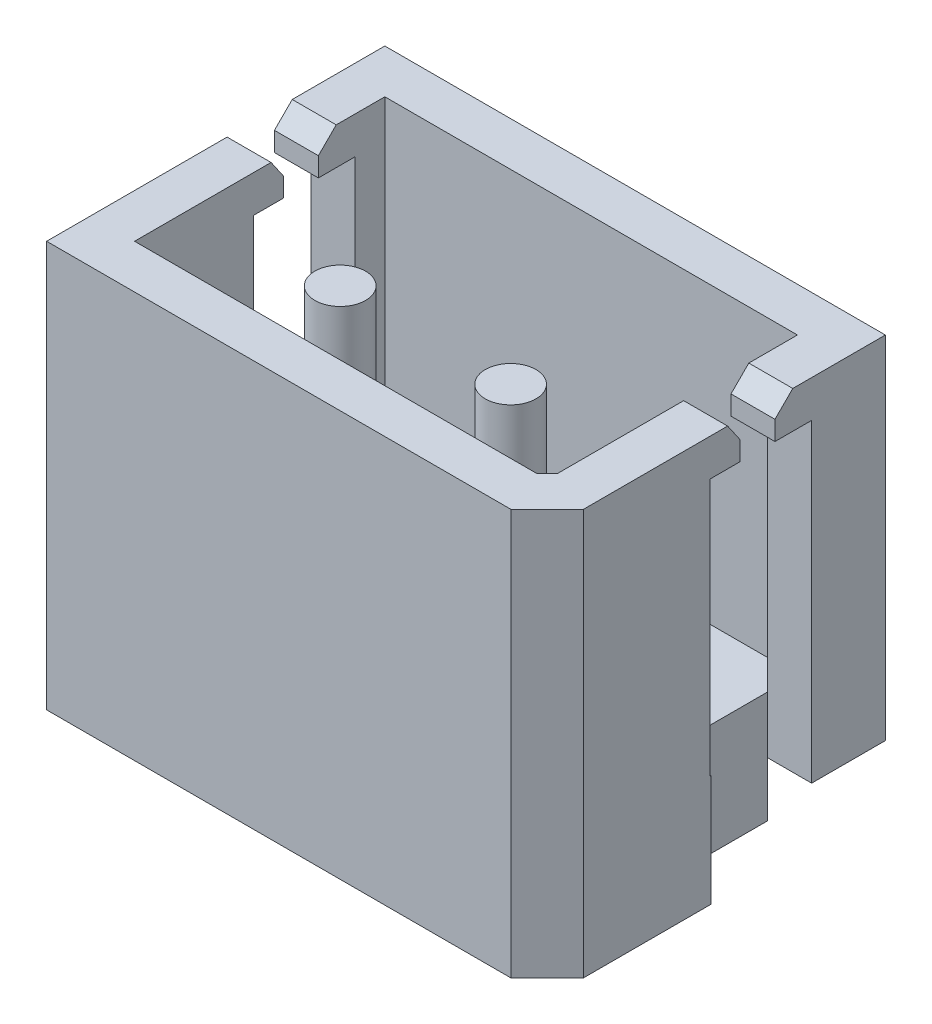
SolidWorks part; units mm, degrees
ref_plane "Front Plane" through (0, 0, 0) normal (0, 0, 1) x (1, 0, 0)
ref_plane "Top Plane" through (0, 0, 0) normal (0, 1, 0) x (1, 0, 0)
ref_plane "Right Plane" through (0, 0, 0) normal (1, 0, 0) x (0, 0, -1)
sketch "Sketch1" plane through (0, 0, 0) normal (0, 1, 0) x (1, 0, 0)
  line L0 (-1.26, 0) -> (0, 0) construction
  line L1 (0, 0) -> (1.26, 0) construction
  circle A0 centre (-1.26, 0) radius 0.375
  circle A1 centre (1.26, 0) radius 0.375
  dimension "D1" = 0.75
  dimension "D2" = 1.26
extrude "Boss-Extrude1" add sketch "Sketch1" along normal blind 5.7 and the other way blind 1
ref_plane "Plane1" through (0, 0, 0) normal (0, 1, 0) x (1, 0, 0)
sketch "Sketch2" plane through (0, 0, 0) normal (0, 1, 0) x (1, 0, 0)
  line L0 (3.7, -1.3656) -> (3.1656, -1.9)
  line L1 (-3.7, -1.9) -> (3.1656, -1.9)
  line L2 (-3.7, -1.9) -> (-3.7, 3.1)
  line L3 (-3.7, 3.1) -> (3.7, 3.1)
  line L4 (3.7, -1.3656) -> (3.7, 3.1)
  line L5 (-3.7, -1.9) -> (3.7, 3.1) construction
  line L6 (-3.7, 3.1) -> (3.7, -1.9) construction
  point P0 (0, 0)
  dimension "D1" = 5
  dimension "D2" = 7.4
  dimension "D3" = 1.9
  dimension "D4" = 3.7
extrude "Boss-Extrude2" add sketch "Sketch2" along normal blind 1.65 contours L2 L3 L4 L0 L1
sketch "Sketch4" plane through (0, 0, 0) normal (0, 1, 0) x (1, 0, 0)
  line L0 (-3.05, -1.25) -> (2.8963, -1.25)
  line L1 (2.8963, -1.25) -> (3.05, -1.0963)
  line L2 (3.05, -1.0963) -> (3.05, 2.45)
  line L3 (3.05, 2.45) -> (-3.05, 2.45)
  line L4 (-3.05, 2.45) -> (-3.05, -1.25)
  line L5 (3.1656, -1.9) -> (3.7, -1.3656)
  line L6 (-3.7, -1.9) -> (3.1656, -1.9)
  line L7 (-3.7, 3.1) -> (-3.7, -1.9)
  line L8 (3.7, 3.1) -> (-3.7, 3.1)
  line L9 (3.7, -1.3656) -> (3.7, 3.1)
  line L10 (3.1656, -1.9) -> (3.7, -1.3656)
  line L11 (-3.7, -1.9) -> (3.1656, -1.9)
  line L12 (-3.7, 3.1) -> (-3.7, -1.9)
  line L13 (3.7, 3.1) -> (-3.7, 3.1)
  line L14 (3.7, -1.3656) -> (3.7, 3.1)
  dimension "D1" = 0
  dimension "D2" = 0.65
extrude "Boss-Extrude4" add sketch "Sketch4" along normal blind 6
ref_plane "Plane2" through (0, 6, 0) normal (0, 1, 0) x (1, 0, 0)
sketch "Sketch5" plane through (0, 6, 0) normal (0, 1, 0) x (1, 0, 0)
  line L1 (-4.2354, 0.5098) -> (4.2354, 0.5098)
  line L2 (-4.2354, 0.5098) -> (-4.2354, 2.0098)
  line L3 (-4.2354, 2.0098) -> (4.2354, 2.0098)
  line L4 (4.2354, 0.5098) -> (4.2354, 2.0098)
  line L5 (-4.2354, 0.5098) -> (4.2354, 2.0098) construction
  line L6 (-4.2354, 2.0098) -> (4.2354, 0.5098) construction
  point P0 (0, 1.2598)
extrude "Cut-Extrude1" cut sketch "Sketch5" along direction (0, 1, 0) on the side against the normal up to surface (4.35 mm away)
ref_plane "Plane3" through (-3.7, 0, 0) normal (-1, 0, 0) x (0, 0, 1)
sketch "Sketch6" plane through (-3.7, 0, 0) normal (-1, 0, 0) x (0, 0, 1)
  line L0 (-2.0098, 6) -> (-1.7311, 6)
  line L1 (-1.7311, 6) -> (-1.4678, 5.7366)
  line L2 (-1.4678, 5.7366) -> (-1.4678, 5.4517)
  line L4 (-1.4678, 5.4517) -> (-2.0098, 5.4517)
  line L5 (-2.0098, 6) -> (-2.0098, 1.65) construction
  line L6 (-2.0098, 5.4517) -> (-2.0098, 6)
  line L7 (-0.5098, 6) -> (-0.7681, 6)
  line L8 (-0.7681, 6) -> (-0.95, 5.7366)
  line L9 (-0.95, 5.7366) -> (-0.95, 5.4517)
  line L10 (-0.95, 5.4517) -> (-0.5098, 5.4517)
  line L11 (-0.5098, 1.65) -> (-0.5098, 6) construction
  line L12 (-0.5098, 5.4517) -> (-0.5098, 6)
extrude "Boss-Extrude5" add sketch "Sketch6" against normal up to surface (0.65 mm away) up to face at (-3.05, 3.825, -2.2299)
ref_plane "Plane4" through (3.7, 0, 0) normal (1, 0, 0) x (0, 0, -1)
sketch "Sketch7" plane through (3.7, 0, 0) normal (1, 0, 0) x (0, 0, -1)
  line L5 (0.7681, 6) -> (0.5098, 6)
  line L6 (0.95, 5.7366) -> (0.7681, 6)
  line L7 (0.95, 5.4517) -> (0.95, 5.7366)
  line L8 (0.5098, 5.4517) -> (0.95, 5.4517)
  line L9 (0.5098, 6) -> (0.5098, 5.4517)
  line L10 (0.7681, 6) -> (0.5098, 6)
  line L11 (0.95, 5.7366) -> (0.7681, 6)
  line L12 (0.95, 5.4517) -> (0.95, 5.7366)
  line L13 (0.5098, 5.4517) -> (0.95, 5.4517)
  line L14 (0.5098, 6) -> (0.5098, 5.4517)
  line L15 (2.0098, 6) -> (1.7311, 6)
  line L16 (1.7311, 6) -> (1.4678, 5.7366)
  line L17 (1.4678, 5.7366) -> (1.4678, 5.4517)
  line L18 (1.4678, 5.4517) -> (2.0098, 5.4517)
  line L19 (2.0098, 5.4517) -> (2.0098, 6)
  line L20 (2.0098, 6) -> (1.7311, 6)
  line L21 (1.7311, 6) -> (1.4678, 5.7366)
  line L22 (1.4678, 5.7366) -> (1.4678, 5.4517)
  line L23 (1.4678, 5.4517) -> (2.0098, 5.4517)
  line L24 (2.0098, 5.4517) -> (2.0098, 6)
  dimension "D1" = 0
  dimension "D2" = 0
extrude "Boss-Extrude6" add sketch "Sketch7" against normal up to surface (0.65 mm away) up to face at (3.05, 3.825, -2.2299)
sketch "Sketch8" plane through (0, 0, 0) normal (1, 0, 0) x (0, 0, -1)
  line L1 (3.7517, -0.5294) -> (2.0098, -0.5294)
  line L2 (3.7517, -0.5294) -> (3.7517, 0.8066)
  line L3 (3.7517, 0.8066) -> (2.0098, 0.8066)
  line L4 (2.0098, -0.5294) -> (2.0098, 0.8066)
extrude "Cut-Extrude2" cut sketch "Sketch8" against normal through all both and the other way through all
ref_plane "Plane5" through (0, 1.65, 0) normal (0, 1, 0) x (1, 0, 0)
sketch "Sketch10" plane through (0, 1.65, 0) normal (0, 1, 0) x (1, 0, 0)
  line L0 (3.7, 0.5098) -> (3.7, 2.0098) construction
  line L1 (3.05, 2.0098) -> (3.7, 2.0098)
  line L2 (3.05, 2.0098) -> (3.05, 0.5211)
  line L3 (3.05, 0.5211) -> (3.7, 0.5211)
  line L4 (3.7, 2.0098) -> (3.7, 0.5211)
  line L6 (-3.7, 2.0098) -> (-3.05, 2.0098)
  line L7 (-3.7, 2.0098) -> (-3.7, 0.5098)
  line L8 (-3.7, 0.5098) -> (-3.05, 0.5098)
  line L9 (-3.05, 2.0098) -> (-3.05, 0.5098)
extrude "Cut-Extrude3" cut sketch "Sketch10" against normal blind 10
